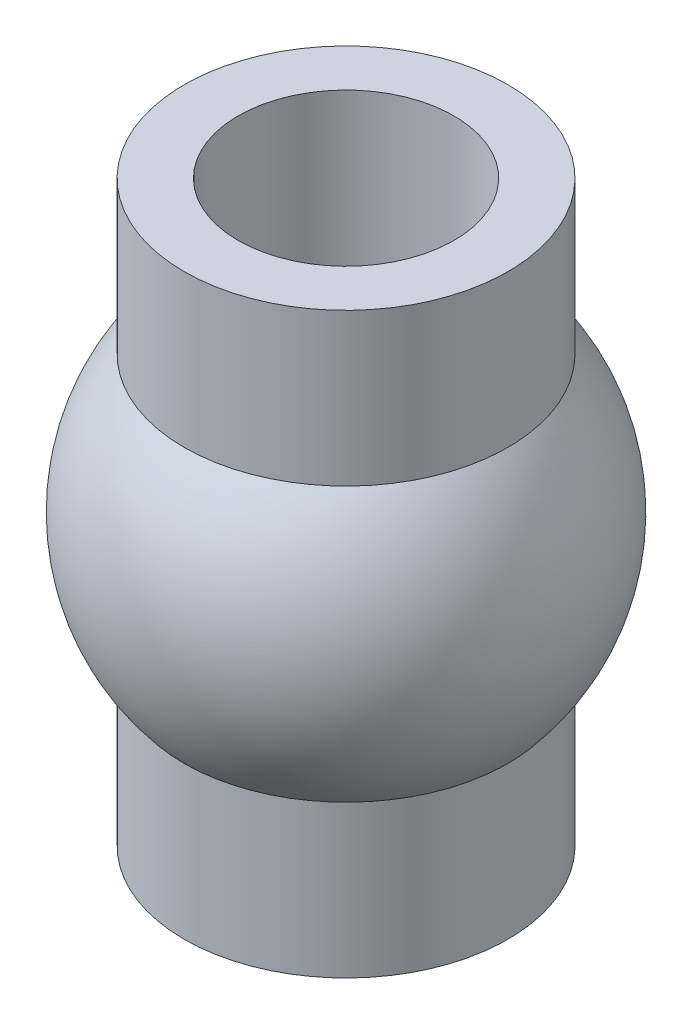
SolidWorks part; units mm, degrees
material "1060 Alloy"
ref_plane "Front Plane" through (0, 0, 0) normal (0, 0, 1) x (1, 0, 0)
ref_plane "Top Plane" through (0, 0, 0) normal (0, 1, 0) x (1, 0, 0)
ref_plane "Right Plane" through (0, 0, 0) normal (1, 0, 0) x (0, 0, -1)
sketch "Sketch1" plane through (0, 0, 0) normal (0, 0, 1) x (1, 0, 0)
  line L0 (0, 0) -> (0, 7.5)
  line L1 (0, 7.5) -> (-2.1, 7.5)
  line L2 (-2.1, 7.5) -> (-2.1, 5.5255)
  line L3 (-2.1, 1.9745) -> (-2.1, 0)
  line L4 (-2.1, 0) -> (0, 0)
  arc A2 (-2.1, 5.5255) -> (-2.1, 1.9745) centre (0, 3.75) ccw
  dimension "D2" = 2.1
  dimension "D4" = 5.5
  dimension "D1" = 7.5
revolve "Revolve1" add sketch "Sketch1" angle 360 about L0
sketch "Sketch2" plane through (0, 7.5, 0) normal (0, 1, 0) x (1, 0, 0)
  circle A0 centre (0, 0) radius 1.4
  circle A1 centre (0, 0) radius 2.1 construction
  dimension "D1" = 0.7
extrude "Cut-Extrude1" cut sketch "Sketch2" against normal up to surface (7.5 mm away) up to face at (0, 0, -2.1)
